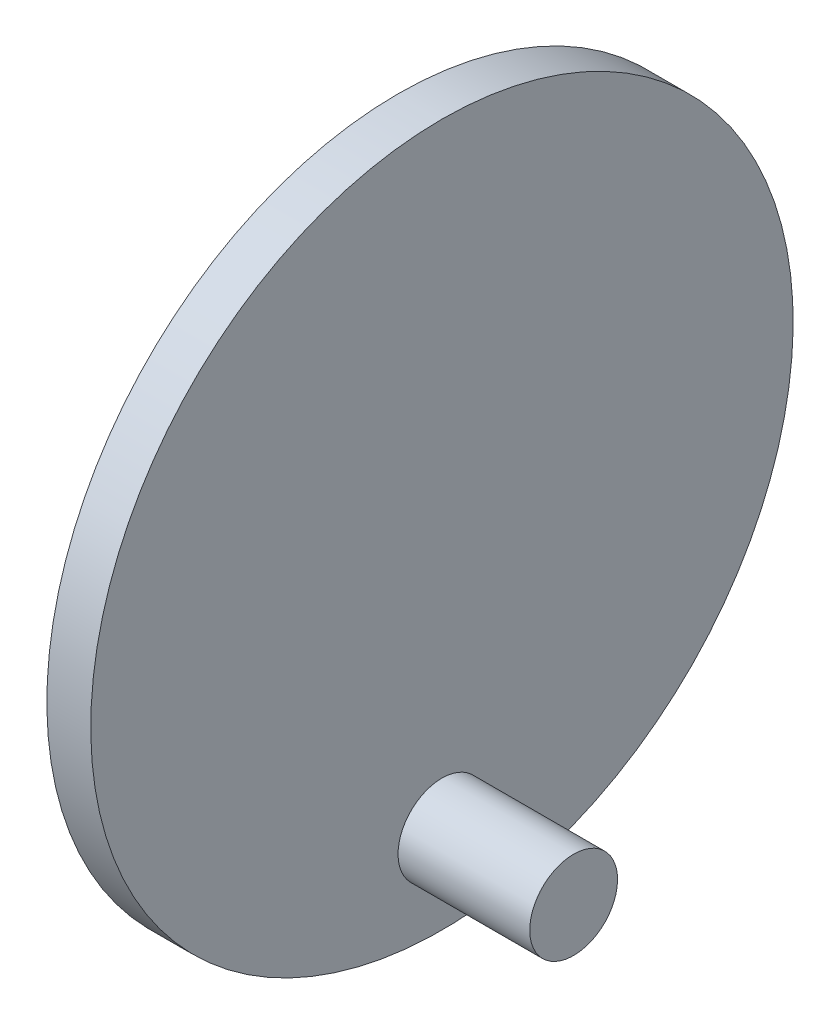
SolidWorks part; units mm, degrees
ref_plane "Front Plane" through (0, 0, 0) normal (0, 0, 1) x (1, 0, 0)
ref_plane "Top Plane" through (0, 0, 0) normal (0, 1, 0) x (1, 0, 0)
ref_plane "Right Plane" through (0, 0, 0) normal (1, 0, 0) x (0, 0, -1)
sketch "Sketch2" plane through (10, 0, 0) normal (1, 0, 0) x (0, 0, -1)
  line L0 (-57.5, 10) -> (57.5, 10) construction
  line L1 (-57.5, 10) -> (-57.5, 150) construction
  circle A0 centre (0, 60) radius 7.5
  dimension "D1" = 15
  dimension "D2" = 50
  dimension "D3" = 57.5
extrude "Boss-Extrude1" add sketch "Sketch2" along normal blind 5 and the other way blind 15
sketch "Sketch3" plane through (15, 0, 0) normal (1, 0, 0) x (0, 0, -1)
  circle A0 centre (0, 60) radius 40
  dimension "D1" = 80
extrude "Boss-Extrude2" add sketch "Sketch3" along normal blind 5
sketch "Sketch4" plane through (20, 0, 0) normal (1, 0, 0) x (0, 0, -1)
  line L0 (0, 60) -> (0, 30) construction
  circle A0 centre (0, 30) radius 5
  dimension "D1" = 10
  dimension "D2" = 30
extrude "Boss-Extrude3" add sketch "Sketch4" along normal blind 15
